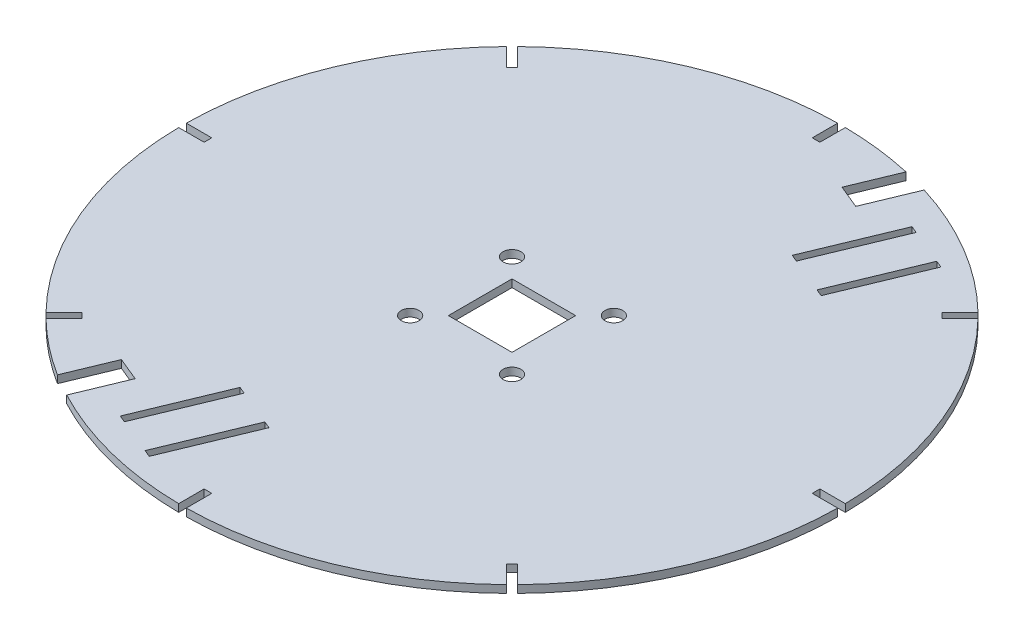
SolidWorks part; units mm, degrees
ref_plane "Front Plane" through (0, 0, 0) normal (0, 0, 1) x (1, 0, 0)
ref_plane "Top Plane" through (0, 0, 0) normal (0, 1, 0) x (1, 0, 0)
ref_plane "Right Plane" through (0, 0, 0) normal (1, 0, 0) x (0, 0, -1)
sketch "Sketch1" plane through (0, 0, 0) normal (0, 1, 0) x (1, 0, 0)
  circle A0 centre (0, 0) radius 129.43
  dimension "D1" = 258.86
extrude "Boss-Extrude1" add sketch "Sketch1" along normal blind 3
sketch "Sketch2" plane through (0, 3, 0) normal (0, 1, 0) x (1, 0, 0)
  line L0 (-1.5, 129.4213) -> (-1.5, 119.4213)
  line L1 (-1.5, 119.4213) -> (1.5, 119.4213)
  line L2 (1.5, 119.4213) -> (1.5, 129.4213)
  circle A0 centre (0, 0) radius 129.43 construction
  dimension "D1" = 10
  dimension "D2" = 10
  dimension "D3" = 3
extrude "Cut-Extrude2" cut sketch "Sketch2" against normal blind 3 and the other way through all contours L0 L1 L2
sketch "Sketch3" plane through (0, 3, 0) normal (0, 1, 0) x (1, 0, 0)
  line L0 (0, 0) -> (0, 76.4749) construction
pattern_circular "CirPattern1" count 8 over 360 about axis through (0, 3, 0) along (0, 0, -1) of "Cut-Extrude2"
sketch "Sketch4" plane through (0, 3, 0) normal (0, 1, 0) x (1, 0, 0)
  line L0 (0, 0) -> (81.131, 0) construction
  line L1 (12.5, -12.5) -> (-12.5, -12.5)
  line L2 (12.5, -12.5) -> (12.5, 12.5)
  line L3 (12.5, 12.5) -> (-12.5, 12.5)
  line L4 (-12.5, -12.5) -> (-12.5, 12.5)
  line L5 (12.5, -12.5) -> (-12.5, 12.5) construction
  line L6 (12.5, 12.5) -> (-12.5, -12.5) construction
  line L7 (0, 0) -> (0, -43.8646) construction
  circle A0 centre (20, 20) radius 3.5
  circle A1 centre (20, -20) radius 3.5
  circle A2 centre (-20, -20) radius 3.5
  circle A3 centre (-20, 20) radius 3.5
  point P0 (0, 0)
  dimension "D3" = 7
  dimension "D1" = 25
  dimension "D2" = 25
  dimension "D4" = 20
  dimension "D5" = 20
extrude "Cut-Extrude3" cut sketch "Sketch4" against normal blind 3
sketch "Sketch5" plane through (0, 3, 0) normal (0, 1, 0) x (1, 0, 0)
  line L0 (-90.454, -92.5753) -> (-1.5, -129.4213) construction
  line L1 (-45.977, -110.9983) -> (0, 0) construction
  line L2 (0, 0) -> (72.9988, -30.2371) construction
  line L3 (-42.7677, -111.0897) -> (-39.9961, -112.2378)
  line L4 (-42.7677, -111.0897) -> (-28.9911, -77.8301)
  line L5 (-28.9911, -77.8301) -> (-26.2194, -78.9781)
  line L6 (-26.2194, -78.9781) -> (-39.9961, -112.2378)
  line L7 (-26.1379, -117.978) -> (-23.3662, -119.1261)
  line L8 (-26.1379, -117.978) -> (-12.3613, -84.7184)
  line L9 (-12.3613, -84.7184) -> (-9.5896, -85.8664)
  line L10 (-9.5896, -85.8664) -> (-23.3662, -119.1261)
  line L11 (53.9358, 67.4976) -> (67.7124, 100.7573)
  line L12 (51.1642, 68.6456) -> (53.9358, 67.4976)
  line L13 (64.9408, 101.9053) -> (51.1642, 68.6456)
  line L14 (64.9408, 101.9053) -> (67.7124, 100.7573)
  line L15 (37.306, 74.3859) -> (51.0826, 107.6456)
  line L16 (34.5344, 75.534) -> (37.306, 74.3859)
  line L17 (48.311, 108.7936) -> (34.5344, 75.534)
  line L18 (48.311, 108.7936) -> (51.0826, 107.6456)
  dimension "D1" = 36
  dimension "D2" = 3
  dimension "D3" = 36
  dimension "D4" = 3
  dimension "D5" = 15
  dimension "D6" = 83
  dimension "D7" = 3
extrude "Cut-Extrude4" cut sketch "Sketch5" against normal blind 10
sketch "Sketch6" plane through (0, 3, 0) normal (0, 1, 0) x (1, 0, 0)
  line L3 (21.1278, 108.4811) -> (30.3562, 104.6586)
  line L4 (30.3562, 104.6586) -> (38.2254, 123.6566)
  line L5 (21.1278, 108.4811) -> (28.4902, 126.2554)
  arc A0 (90.454, 92.5753) -> (1.5, 129.4213) centre (0, 0) ccw construction
  point P11 (25.742, 106.5698)
  point P12 (25.742, 106.5698)
  dimension "D1" = 17.7744
  dimension "D2" = 7.3624
  dimension "D3" = 9.9887
  dimension "D4" = 20.5633
extrude "Cut-Extrude5" cut sketch "Sketch6" against normal blind 3 and the other way through all flip side to cut
sketch "Sketch8" plane through (0, 3, 0) normal (0, 1, 0) x (1, 0, 0)
  line L3 (-61.7525, -91.6538) -> (-52.5553, -95.4634)
  line L4 (-61.7525, -91.6538) -> (-69.116, -109.4308)
  line L5 (-52.5553, -95.4634) -> (-60.4239, -114.4599)
  arc A0 (-90.454, -92.5753) -> (-1.5, -129.4213) centre (0, 0) ccw construction
  point P11 (-57.1539, -93.5586)
  dimension "D1" = 17.777
  dimension "D2" = 7.3635
  dimension "D3" = 9.955
  dimension "D4" = 20.5617
extrude "Cut-Extrude6" cut sketch "Sketch8" against normal blind 3 and the other way through all flip side to cut
sketch "Sketch9" plane through (0, 3, 0) normal (0, 1, 0) x (1, 0, 0)
  text T0 "B3" font "Century Gothic" height in points 22
  dimension "D1" = 4
  dimension "D2" = 16
